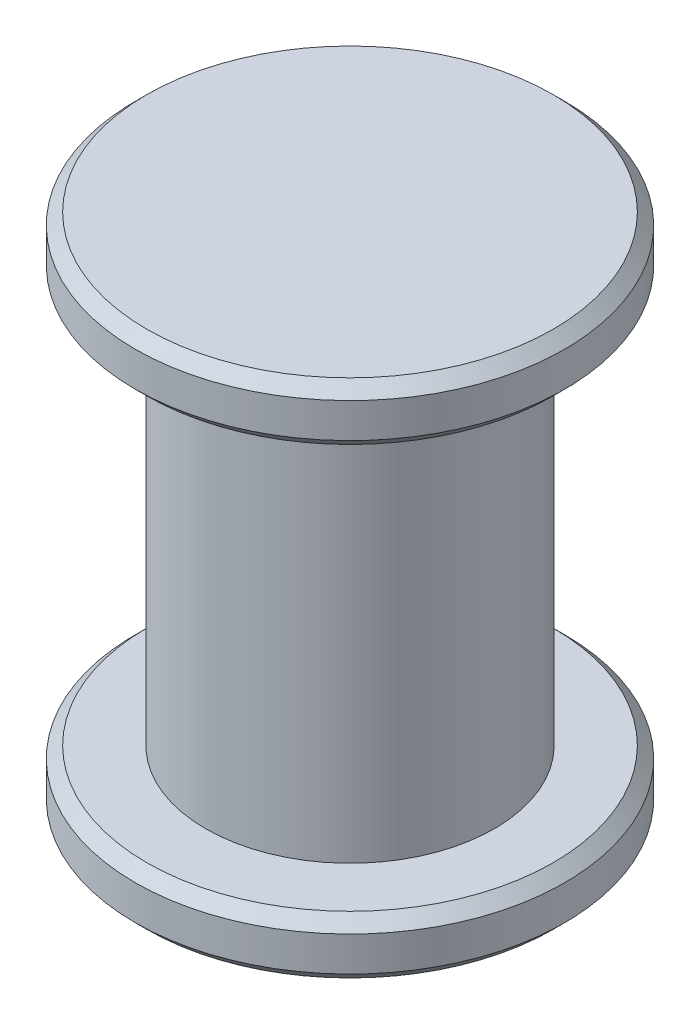
SolidWorks part; units mm, degrees
ref_plane "Front Plane" through (0, 0, 0) normal (0, 0, 1) x (1, 0, 0)
ref_plane "Top Plane" through (0, 0, 0) normal (0, 1, 0) x (1, 0, 0)
ref_plane "Right Plane" through (0, 0, 0) normal (1, 0, 0) x (0, 0, -1)
sketch "Sketch2" plane through (0, 0, 0) normal (0, 1, 0) x (1, 0, 0)
  circle A0 centre (0, 0) radius 0.25
  dimension "D1" = 0.5
extrude "Boss-Extrude1" add sketch "Sketch2" along normal blind 0.7
sketch "Sketch3" plane through (0, 0.7, 0) normal (0, 1, 0) x (1, 0, 0)
  circle A0 centre (0, 0) radius 0.3719
extrude "Boss-Extrude2" add sketch "Sketch3" along normal blind 0.1
sketch "Sketch4" plane through (0, 0, 0) normal (0, -1, 0) x (1, 0, 0)
  circle A0 centre (0, 0) radius 0.3719
extrude "Boss-Extrude3" add sketch "Sketch4" along normal blind 0.1
chamfer "Chamfer1" distance 0.02 angle 45 1 edges at (0, 0.8, 0.3719)
chamfer "Chamfer2" distance 0.02 angle 45 2 edges at (0, 0, -0.3719) (0, 0.7, 0.3719)
chamfer "Chamfer3" distance 0.02 angle 45 1 edges at (0, -0.1, -0.3719)
